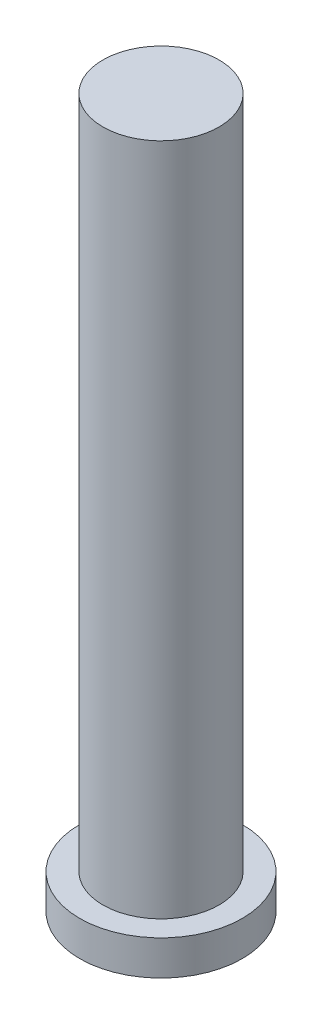
SolidWorks part; units mm, degrees
ref_plane "Front" through (0, 0, 0) normal (0, 0, 1) x (1, 0, 0)
ref_plane "Top" through (0, 0, 0) normal (0, 1, 0) x (1, 0, 0)
ref_plane "Right" through (0, 0, 0) normal (1, 0, 0) x (0, 0, -1)
other "Configuration Table"
sketch "Эскиз1" plane through (0, 0, 0) normal (0, 1, 0) x (1, 0, 0)
  circle A0 centre (0, 0) radius 7
extrude "Бобышка-Вытянуть1" add sketch "Эскиз1" along normal blind 3
sketch "Эскиз2" plane through (0, 3, 0) normal (0, 1, 0) x (1, 0, 0)
  circle A0 centre (0, 0) radius 5
extrude "Бобышка-Вытянуть2" add sketch "Эскиз2" along normal blind 58
